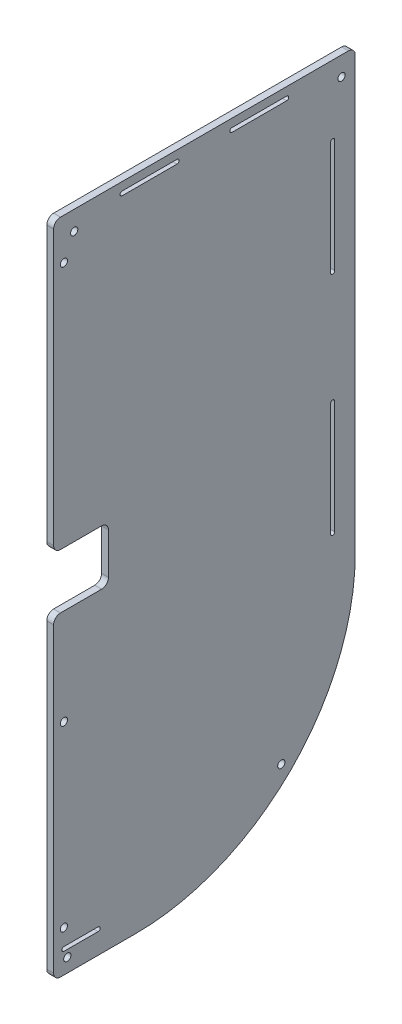
SolidWorks part; units mm, degrees
material "PC High Viscosity"
ref_plane "Front Plane" through (0, 0, 0) normal (0, 0, 1) x (1, 0, 0)
ref_plane "Top Plane" through (0, 0, 0) normal (0, 1, 0) x (1, 0, 0)
ref_plane "Right Plane" through (0, 0, 0) normal (1, 0, 0) x (0, 0, -1)
sketch "Sketch1" plane through (0, 0, 0) normal (1, 0, 0) x (0, 0, -1)
  line L0 (0, 0) -> (0, -609.6)
  line L1 (0, -609.6) -> (76.2, -609.6)
  line L2 (279.4, -406.4) -> (279.4, 0)
  line L3 (0, 0) -> (279.4, 0)
  arc A0 (76.2, -609.6) -> (279.4, -406.4) centre (76.2, -406.4) ccw
  dimension "D1" = 279.4
  dimension "D2" = 203.2
  dimension "D3" = 609.6
extrude "Boss-Extrude1" add sketch "Sketch1" along normal blind 6.35
sketch "Sketch2" plane through (6.35, 0, 0) normal (1, 0, 0) x (0, 0, -1)
  line L0 (279.4, 0) -> (0, 0) construction
  line L1 (279.4, -406.4) -> (279.4, 0) construction
  line L2 (76.2, -406.4) -> (210.9038, -541.1038) construction
  line L3 (0, 0) -> (0, -609.6) construction
  line L4 (0, -609.6) -> (76.2, -609.6) construction
  circle A0 centre (266.7, -17.78) radius 3.3655
  circle A2 centre (12.7, -596.9) radius 3.3655
  circle A3 centre (210.9038, -541.1038) radius 3.3655
  circle A4 centre (19.05, -17.78) radius 3.3655
  circle A6 centre (76.2, -406.4) radius 190.5 construction
  dimension "D1" = 17.78
  dimension "D3" = 6.731
  dimension "D4" = 381
  dimension "D8" = 247.65
  dimension "D2" = 12.7
  dimension "D5" = 45
  dimension "D6" = 12.7
  dimension "D7" = 12.7
extrude "Cut-Extrude1" cut sketch "Sketch2" against normal through all
fillet "Fillet1" radius 6.35 3 edges at (3.175, -609.6, 0) (3.175, 0, -279.4) (3.175, 0, 0)
sketch "Sketch3" plane through (6.35, 0, 0) normal (1, 0, 0) x (0, 0, -1)
  line L2 (63.5, -9.525) -> (114.3, -9.525) construction
  line L3 (63.5, -7.62) -> (114.3, -7.62)
  line L4 (63.5, -11.43) -> (114.3, -11.43)
  line L5 (165.1, -9.525) -> (215.9, -9.525) construction
  line L6 (165.1, -7.62) -> (215.9, -7.62)
  line L7 (165.1, -11.43) -> (215.9, -11.43)
  line L8 (0, -6.35) -> (0, -603.25) construction
  line L9 (273.05, 0) -> (6.35, 0) construction
  arc A2 (63.5, -7.62) -> (63.5, -11.43) centre (63.5, -9.525) ccw
  arc A3 (114.3, -11.43) -> (114.3, -7.62) centre (114.3, -9.525) ccw
  arc A4 (165.1, -7.62) -> (165.1, -11.43) centre (165.1, -9.525) ccw
  arc A5 (215.9, -11.43) -> (215.9, -7.62) centre (215.9, -9.525) ccw
  point P2 (88.9, -9.525)
  point P8 (190.5, -9.525)
  dimension "D1" = 50.8
  dimension "D4" = 9.525
  dimension "D2" = 88.9
  dimension "D3" = 101.6
  dimension "D5" = 3.81
extrude "Cut-Extrude6" cut sketch "Sketch3" against normal through all
sketch "Sketch4" plane through (6.35, 0, 0) normal (1, 0, 0) x (0, 0, -1)
  line L0 (273.05, 0) -> (6.35, 0) construction
  line L1 (6.35, -609.6) -> (76.2, -609.6) construction
  line L2 (0, -6.35) -> (0, -603.25) construction
  circle A0 centre (9.525, -38.1) radius 3.3655
  circle A1 centre (9.525, -406.4) radius 3.3655
  circle A2 centre (9.525, -571.5) radius 3.3655
  dimension "D1" = 6.731
  dimension "D2" = 38.1
  dimension "D3" = 38.1
  dimension "D4" = 165.1
  dimension "D5" = 9.525
extrude "Cut-Extrude3" cut sketch "Sketch4" against normal through all
sketch "Sketch6" plane through (6.35, 0, 0) normal (1, 0, 0) x (0, 0, -1)
  line L0 (258.445, -65.0875) -> (258.445, -169.8625) construction
  line L1 (260.35, -65.0875) -> (260.35, -169.8625)
  line L2 (256.54, -65.0875) -> (256.54, -169.8625)
  line L3 (279.4, -406.4) -> (279.4, -6.35) construction
  line L4 (273.05, 0) -> (6.35, 0) construction
  line L5 (258.445, -379.4125) -> (258.445, -274.6375) construction
  line L6 (256.54, -379.4125) -> (256.54, -274.6375)
  line L7 (260.35, -379.4125) -> (260.35, -274.6375)
  arc A0 (260.35, -65.0875) -> (256.54, -65.0875) centre (258.445, -65.0875) ccw
  arc A1 (256.54, -169.8625) -> (260.35, -169.8625) centre (258.445, -169.8625) ccw
  arc A2 (256.54, -379.4125) -> (260.35, -379.4125) centre (258.445, -379.4125) ccw
  arc A3 (260.35, -274.6375) -> (256.54, -274.6375) centre (258.445, -274.6375) ccw
  point P2 (258.445, -117.475)
  point P13 (258.445, -327.025)
  dimension "D1" = 3.81
  dimension "D2" = 19.05
  dimension "D3" = 104.775
  dimension "D4" = 117.475
  dimension "D5" = 327.025
extrude "Cut-Extrude7" cut sketch "Sketch6" against normal through all
sketch "Sketch7" plane through (6.35, 0, 0) normal (1, 0, 0) x (0, 0, -1)
  line L0 (9.525, -588.645) -> (41.275, -588.645) construction
  line L1 (9.525, -586.74) -> (41.275, -586.74)
  line L2 (9.525, -590.55) -> (41.275, -590.55)
  line L3 (6.35, -609.6) -> (76.2, -609.6) construction
  line L4 (0, -6.35) -> (0, -603.25) construction
  arc A0 (9.525, -586.74) -> (9.525, -590.55) centre (9.525, -588.645) ccw
  arc A1 (41.275, -590.55) -> (41.275, -586.74) centre (41.275, -588.645) ccw
  point P2 (25.4, -588.645)
  dimension "D1" = 19.05
  dimension "D2" = 3.81
  dimension "D3" = 25.4
  dimension "D4" = 31.75
extrude "Cut-Extrude8" cut sketch "Sketch7" against normal through all and the other way through all
sketch "Sketch8" plane through (6.35, 0, 0) normal (1, 0, 0) x (0, 0, -1)
  line L0 (0, -6.35) -> (0, -603.25) construction
  line L1 (0, -266.7) -> (50.8, -266.7)
  line L2 (0, -266.7) -> (0, -317.5)
  line L3 (0, -317.5) -> (50.8, -317.5)
  line L4 (50.8, -266.7) -> (50.8, -317.5)
  line L5 (273.05, 0) -> (6.35, 0) construction
  dimension "D1" = 266.7
  dimension "D2" = 50.8
  dimension "D3" = 50.8
extrude "Cut-Extrude9" cut sketch "Sketch8" against normal through all
fillet "Fillet2" radius 6.35 4 edges at (3.175, -317.5, 0) (3.175, -317.5, -50.8) (3.175, -266.7, -50.8) (3.175, -266.7, 0)
